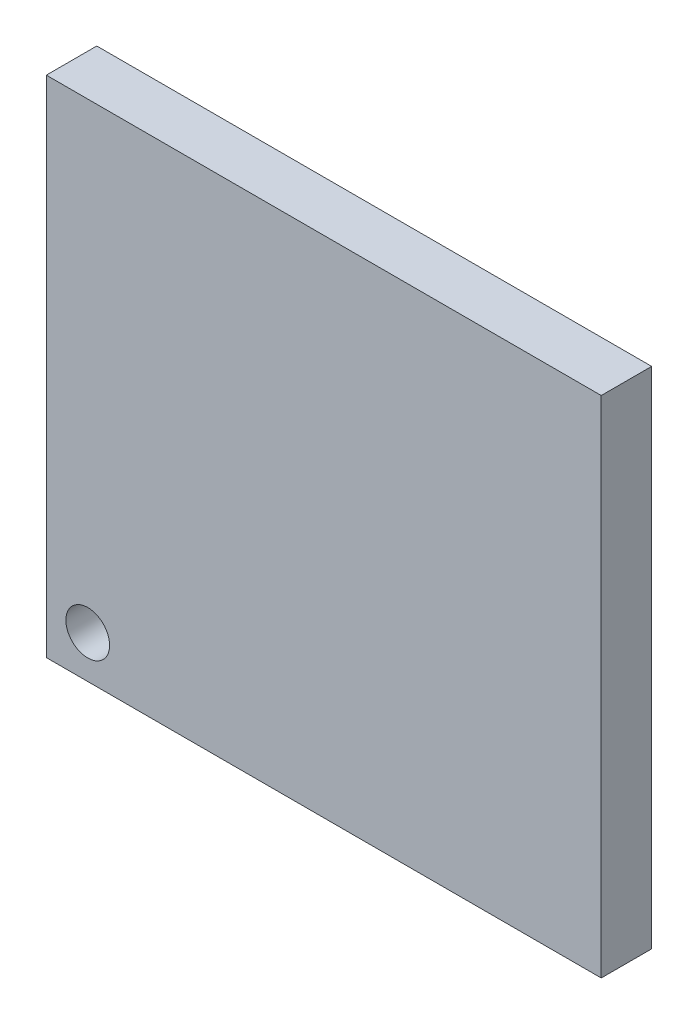
SolidWorks part; units mm, degrees
ref_plane "Plan de face" through (0, 0, 0) normal (0, 0, 1) x (1, 0, 0)
ref_plane "Plan de dessus" through (0, 0, 0) normal (0, 1, 0) x (1, 0, 0)
ref_plane "Plan de droite" through (0, 0, 0) normal (1, 0, 0) x (0, 0, -1)
sketch "Esquisse1" plane through (0, 0, 0) normal (0, 0, 1) x (1, 0, 0)
  line L17 (-16.5, 15) -> (16.5, 15)
  line L18 (-16.5, 15) -> (-16.5, -15)
  line L19 (-16.5, -15) -> (16.5, -15)
  line L20 (16.5, 15) -> (16.5, -15)
  line L21 (-16.5, 15) -> (16.5, -15) construction
  line L22 (-16.5, -15) -> (16.5, 15) construction
  point P0 (0, 0)
  dimension "D1" = 30
  dimension "D2" = 33
extrude "Boss.-Extru.1" add sketch "Esquisse1" along normal blind 3
hole_wizard "Dégagement M1.61" positions "Esquisse2" profile "Esquisse3" hole size "M1.6" standard "Ansi Metric"
sketch "Esquisse2" plane through (0, 0, 3) normal (0, 0, 1) x (1, 0, 0)
  point P0 (-14.0363, -12.486)
sketch "Esquisse3" plane through (-14.0363, -12.486, 3) normal (1, 0, 0) x (0, -1, 0)
  line L0 (0, 0) -> (0, 50)
  line L1 (0, 50) -> (1.3, 50)
  line L2 (1.3, 50) -> (1.3, 0)
  line L5 (1.3, 0) -> (0, 0)
  line L10 (0, 50) -> (-1.3, 50) construction
  line L11 (0, -6.35) -> (0, 107.95) construction
  dimension "Diamètre du perçage" = 2.6
  dimension "Profondeur du perçage" = 50
  dimension "Angle de pointe" = 180
